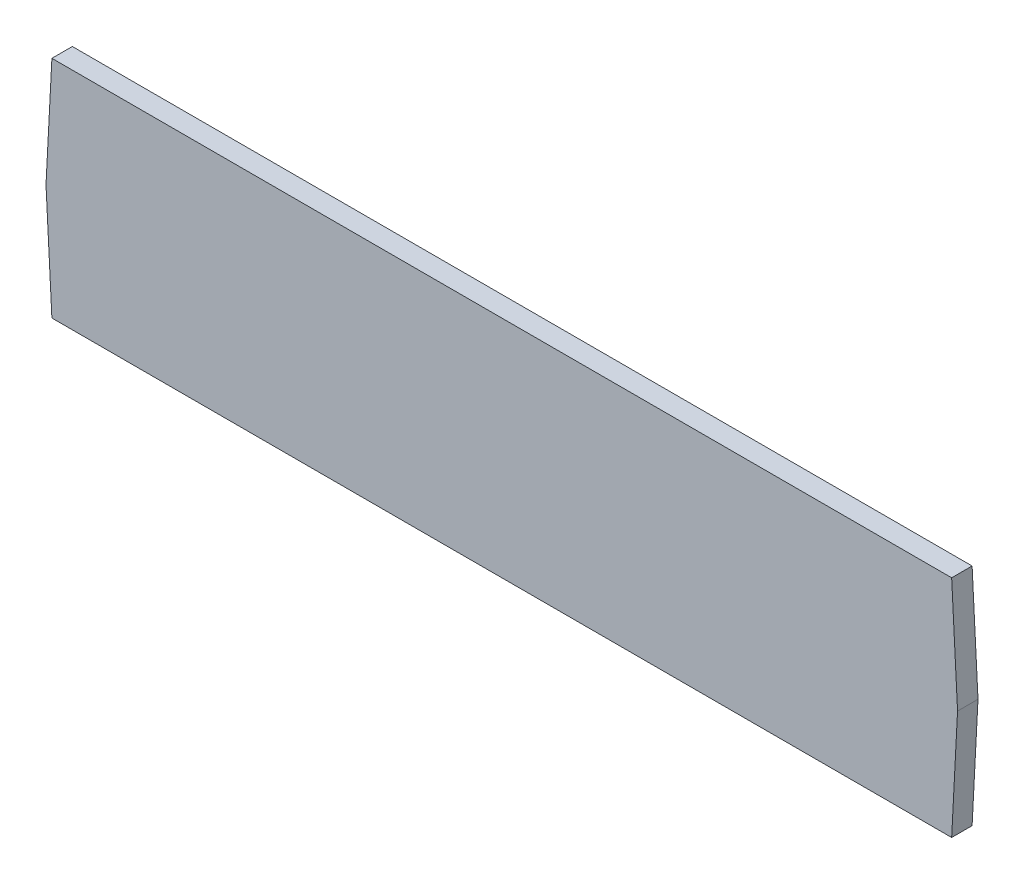
SolidWorks part; units mm, degrees
ref_plane "Front Plane" through (0, 0, 0) normal (0, 0, 1) x (1, 0, 0)
ref_plane "Top Plane" through (0, 0, 0) normal (0, 1, 0) x (1, 0, 0)
ref_plane "Right Plane" through (0, 0, 0) normal (1, 0, 0) x (0, 0, -1)
sketch "Sketch1" plane through (0, 0, 0) normal (0, 0, 1) x (1, 0, 0)
  line L0 (0, 0) -> (132, 0)
  line L1 (132, 0) -> (132.8647, -16.5)
  line L2 (132, -33) -> (0, -33)
  line L3 (0, 0) -> (-0.8647, -16.5)
  line L4 (0, -33) -> (-0.8647, -16.5)
  line L5 (132, -33) -> (132.8647, -16.5)
extrude "Boss-Extrude1" add sketch "Sketch1" along normal blind 3
sketch "Esboço1" plane through (0, 0, 3) normal (0, 0, 1) x (1, 0, 0)
  line L0 (0, 0) -> (132, 0) construction
  line L2 (0.0023, -33.0441) -> (132.0023, -33.0441)
  line L3 (129.5891, 0) -> (129.5891, -33)
  line L5 (0.0023, -33.0441) -> (-0.8647, -16.5)
  circle A0 centre (15.2648, -16.5) radius 3.05
  circle A1 centre (29.3449, -16.5) radius 3.55
  circle A2 centre (43.4322, -16.5) radius 4.05
  circle A3 centre (57.5192, -16.5) radius 4.05
  circle A4 centre (71.597, -16.5) radius 4.05
  circle A5 centre (86.5962, -2.1588) radius 1.55
  circle A6 centre (116.9962, -2.1588) radius 1.55
  circle A7 centre (86.5962, -30.8412) radius 1.55
  circle A8 centre (116.9962, -30.8412) radius 1.55
  dimension "D1" = 16.5
  dimension "D3" = 86.5962
  dimension "D6" = 6.1
  dimension "D7" = 7.1
  dimension "D8" = 8.1
  dimension "D9" = 8.1
  dimension "D10" = 8.1
  dimension "D11" = 3.1
  dimension "D12" = 3.1
  dimension "D13" = 3.1
  dimension "D14" = 3.1
  dimension "D2" = 14.0801
  dimension "D4" = 30.4
  dimension "D5" = 2.1588
  dimension "D15" = 33
  dimension "D16" = 132
  dimension "D17" = 93
  dimension "D18" = 15.2625
other "Alinhar grupo1"
other "Alinhar grupo2"
